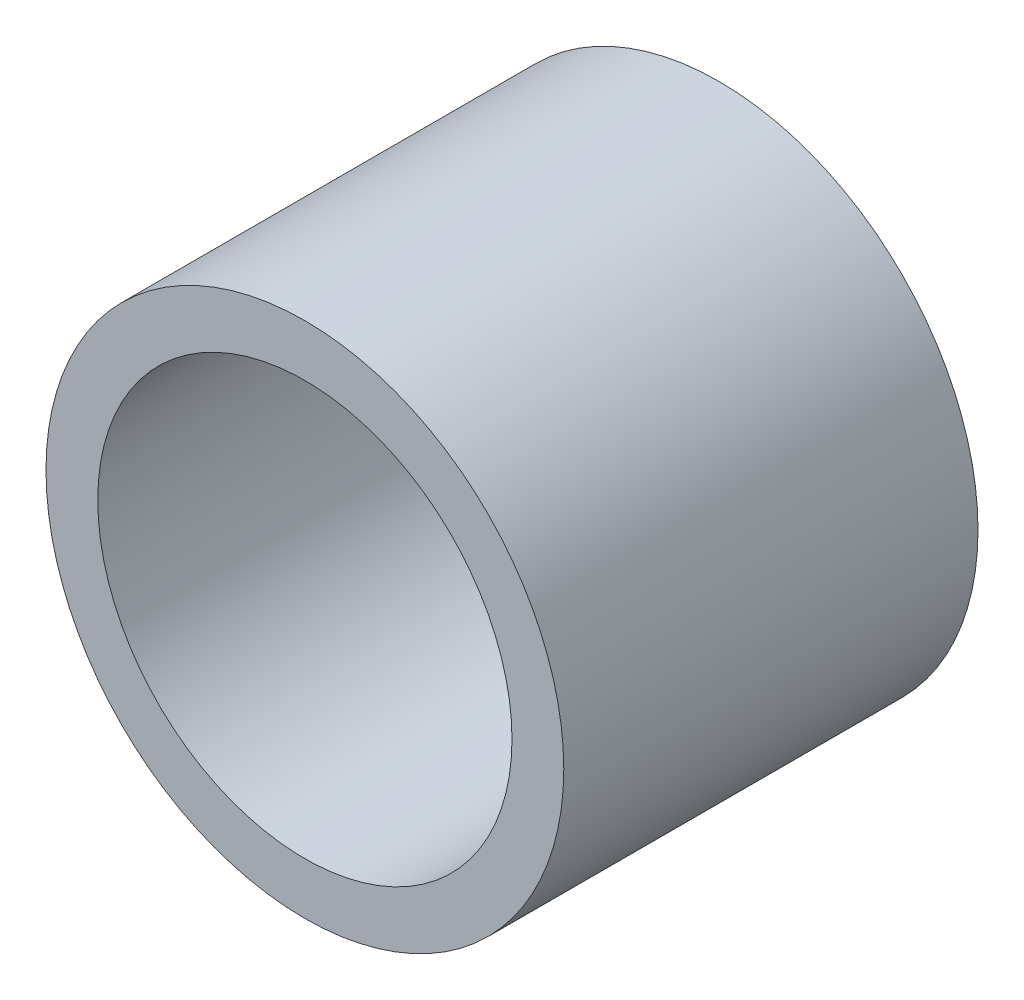
SolidWorks part; units mm, degrees
ref_plane "Front Plane" through (0, 0, 0) normal (0, 0, 1) x (1, 0, 0)
ref_plane "Top Plane" through (0, 0, 0) normal (0, 1, 0) x (1, 0, 0)
ref_plane "Right Plane" through (0, 0, 0) normal (1, 0, 0) x (0, 0, -1)
ref_plane "Plane1" through (0, 0, 0) normal (0, -1, 0) x (1, 0, 0)
sketch "Sketch1" plane through (0, 0, 0) normal (0, -1, 0) x (1, 0, 0)
  line L0 (3.175, -3.175) -> (3.9688, -3.175)
  line L1 (3.9688, -3.175) -> (3.9688, 3.175)
  line L2 (3.9688, 3.175) -> (3.175, 3.175)
  line L3 (3.175, 3.175) -> (3.175, -3.175)
  line L4 (0, 3.175) -> (0, -3.175) construction
revolve "Revolve1" add sketch "Sketch1" angle 360 about L4
